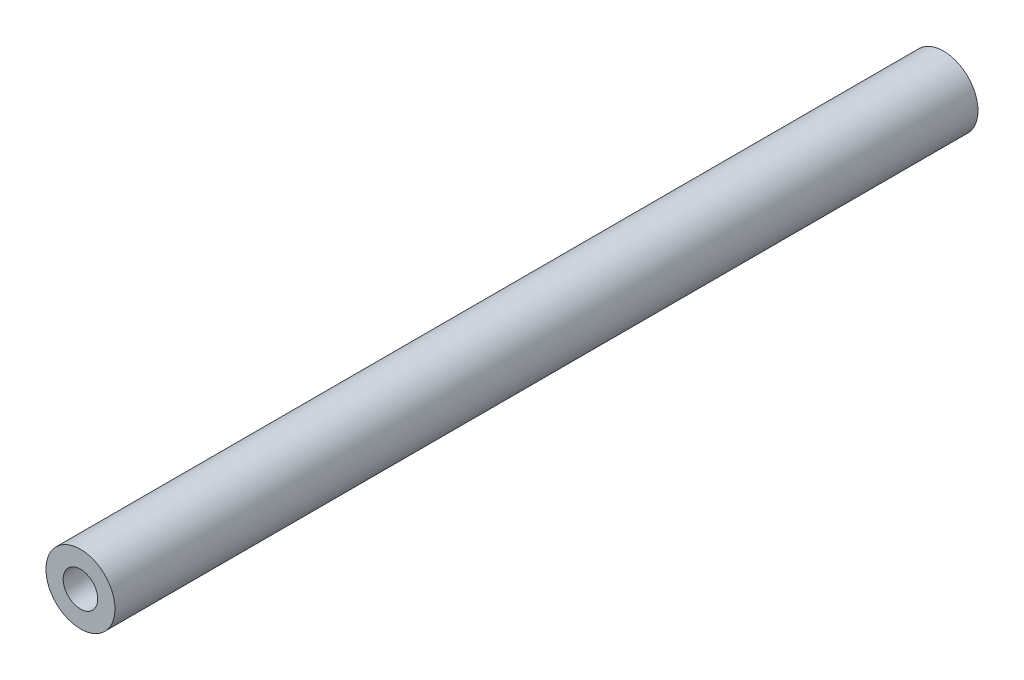
SolidWorks part; units mm, degrees
material "Thornel Mat VMA"
ref_plane "Front Plane" through (0, 0, 0) normal (0, 0, 1) x (1, 0, 0)
ref_plane "Top Plane" through (0, 0, 0) normal (0, 1, 0) x (1, 0, 0)
ref_plane "Right Plane" through (0, 0, 0) normal (1, 0, 0) x (0, 0, -1)
sketch "Sketch1" plane through (0, 0, 0) normal (0, 0, 1) x (1, 0, 0)
  circle A0 centre (0, 0) radius 2
  circle A1 centre (0, 0) radius 1
  dimension "D1" = 4
  dimension "D2" = 1
extrude "Boss-Extrude1" add sketch "Sketch1" along normal blind 50
